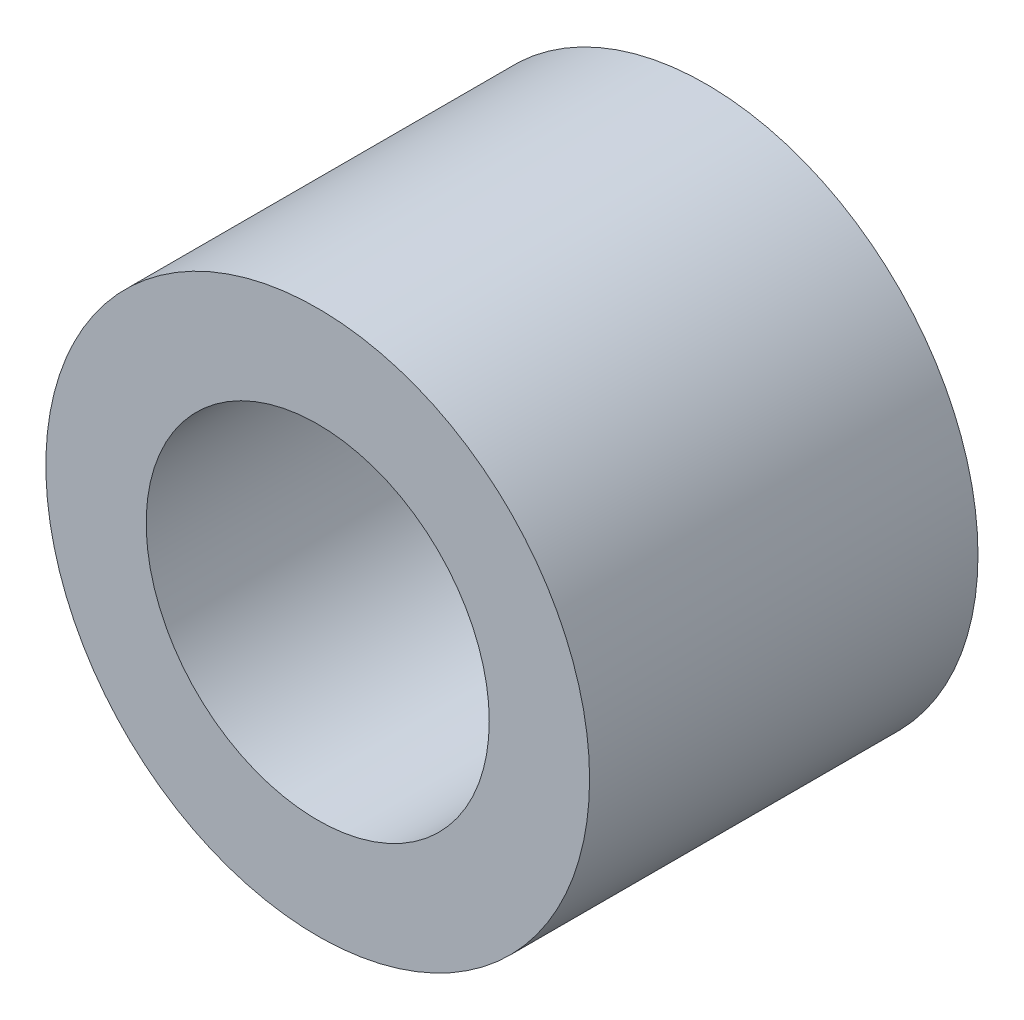
SolidWorks part; units mm, degrees
material "Латунь"
ref_plane "Спереди" through (0, 0, 0) normal (0, 0, 1) x (1, 0, 0)
ref_plane "Сверху" through (0, 0, 0) normal (0, 1, 0) x (1, 0, 0)
ref_plane "Справа" through (0, 0, 0) normal (1, 0, 0) x (0, 0, -1)
sketch "Эскиз7" plane through (0, 0, 0) normal (1, 0, 0) x (0, 0, -1)
  line L1 (0, 0) -> (3, 0)
  line L2 (0, 0) -> (0, 1.9)
  line L3 (0, 1.9) -> (3, 1.9)
  line L4 (3, 0) -> (3, 1.9)
  dimension "D1" = 3
  dimension "D2" = 1.9
revolve "Повернуть1" add sketch "Эскиз7" angle 360 about L1
hole_wizard "Отверстие обработанное метчиком M3x0.351" positions "Эскиз8" profile "Эскиз9" tap size "M3x0.35" standard "DIN" end condition through all
sketch "Эскиз8" plane through (0, 0, 0) normal (0, 0, 1) x (1, 0, 0)
  point P0 (0, 0)
sketch "Эскиз9" plane through (0, 0, 0) normal (1, 0, 0) x (0, -1, 0)
  line L0 (0, 0) -> (0, 3)
  line L1 (0, 3) -> (1.325, 3)
  line L2 (1.325, 3) -> (1.325, 0)
  line L5 (1.325, 0) -> (0, 0)
  line L11 (0, -6.35) -> (0, 107.95) construction
  dimension "Диаметр проходного сверла" = 2.65
  dimension "Глубина проходного сверла" = 3
cosmetic thread "Отверстие резьбы2" parameters "D2"=3
sketch "Эскиз45" plane through (0, 0, 0) normal (0, 0, 1) x (1, 0, 0)
  line L0 (0, 0) -> (0, 1.9) construction
  line L1 (0, 0.0356) -> (0, 0) construction
  line L2 (0, 0) -> (0.3647, 2.0681) construction
  line L3 (0, 2.1) -> (0, 0) construction
  line L4 (0, 2.1) -> (0, 1.8)
  line L5 (0.3126, 1.7727) -> (0.3647, 2.0681)
  line L6 (0.7182, 1.9734) -> (0.6156, 1.6914)
  line L7 (0.9, 1.5588) -> (1.05, 1.8187)
  line L8 (1.3499, 1.6087) -> (1.157, 1.3789)
  line L9 (1.3789, 1.157) -> (1.6087, 1.3499)
  line L10 (1.8187, 1.05) -> (1.5588, 0.9)
  line L11 (1.6914, 0.6156) -> (1.9734, 0.7182)
  line L12 (2.0681, 0.3647) -> (1.7727, 0.3126)
  line L13 (1.8, 0) -> (2.1, 0)
  line L14 (2.0681, -0.3647) -> (1.7727, -0.3126)
  line L15 (1.6914, -0.6156) -> (1.9734, -0.7182)
  line L16 (1.8187, -1.05) -> (1.5588, -0.9)
  line L17 (1.3789, -1.157) -> (1.6087, -1.3499)
  line L18 (1.3499, -1.6087) -> (1.157, -1.3789)
  line L19 (0.9, -1.5588) -> (1.05, -1.8187)
  line L20 (0.7182, -1.9734) -> (0.6156, -1.6914)
  line L21 (0.3126, -1.7727) -> (0.3647, -2.0681)
  line L22 (0, -2.1) -> (0, -1.8)
  line L23 (-0.3126, -1.7727) -> (-0.3647, -2.0681)
  line L24 (-0.7182, -1.9734) -> (-0.6156, -1.6914)
  line L25 (-0.9, -1.5588) -> (-1.05, -1.8187)
  line L26 (-1.3499, -1.6087) -> (-1.157, -1.3789)
  line L27 (-1.3789, -1.157) -> (-1.6087, -1.3499)
  line L28 (-1.8187, -1.05) -> (-1.5588, -0.9)
  line L29 (-1.6914, -0.6156) -> (-1.9734, -0.7182)
  line L30 (-2.0681, -0.3647) -> (-1.7727, -0.3126)
  line L31 (-1.8, 0) -> (-2.1, 0)
  line L32 (-2.0681, 0.3647) -> (-1.7727, 0.3126)
  line L33 (-1.6914, 0.6156) -> (-1.9734, 0.7182)
  line L34 (-1.8187, 1.05) -> (-1.5588, 0.9)
  line L35 (-1.3789, 1.157) -> (-1.6087, 1.3499)
  line L36 (-1.3499, 1.6087) -> (-1.157, 1.3789)
  line L37 (-0.9, 1.5588) -> (-1.05, 1.8187)
  line L38 (-0.7182, 1.9734) -> (-0.6156, 1.6914)
  line L39 (-0.3126, 1.7727) -> (-0.3647, 2.0681)
  arc A0 (0, 2.1) -> (0.3647, 2.0681) centre (0, 0) cw
  arc A1 (0.7182, 1.9734) -> (1.05, 1.8187) centre (0, 0) cw
  arc A2 (0.3126, 1.7727) -> (0, 1.8) centre (0, 0) ccw
  arc A3 (0.9, 1.5588) -> (0.6156, 1.6914) centre (0, 0) ccw
  arc A4 (1.3499, 1.6087) -> (1.6087, 1.3499) centre (0, 0) cw
  arc A5 (1.3789, 1.157) -> (1.157, 1.3789) centre (0, 0) ccw
  arc A6 (1.8187, 1.05) -> (1.9734, 0.7182) centre (0, 0) cw
  arc A7 (1.6914, 0.6156) -> (1.5588, 0.9) centre (0, 0) ccw
  arc A8 (2.0681, 0.3647) -> (2.1, 0) centre (0, 0) cw
  arc A9 (1.8, 0) -> (1.7727, 0.3126) centre (0, 0) ccw
  arc A10 (2.0681, -0.3647) -> (1.9734, -0.7182) centre (0, 0) cw
  arc A11 (1.6914, -0.6156) -> (1.7727, -0.3126) centre (0, 0) ccw
  arc A12 (1.8187, -1.05) -> (1.6087, -1.3499) centre (0, 0) cw
  arc A13 (1.3789, -1.157) -> (1.5588, -0.9) centre (0, 0) ccw
  arc A14 (1.3499, -1.6087) -> (1.05, -1.8187) centre (0, 0) cw
  arc A15 (0.9, -1.5588) -> (1.157, -1.3789) centre (0, 0) ccw
  arc A16 (0.7182, -1.9734) -> (0.3647, -2.0681) centre (0, 0) cw
  arc A17 (0.3126, -1.7727) -> (0.6156, -1.6914) centre (0, 0) ccw
  arc A18 (0, -2.1) -> (-0.3647, -2.0681) centre (0, 0) cw
  arc A19 (-0.3126, -1.7727) -> (0, -1.8) centre (0, 0) ccw
  arc A20 (-0.7182, -1.9734) -> (-1.05, -1.8187) centre (0, 0) cw
  arc A21 (-0.9, -1.5588) -> (-0.6156, -1.6914) centre (0, 0) ccw
  arc A22 (-1.3499, -1.6087) -> (-1.6087, -1.3499) centre (0, 0) cw
  arc A23 (-1.3789, -1.157) -> (-1.157, -1.3789) centre (0, 0) ccw
  arc A24 (-1.8187, -1.05) -> (-1.9734, -0.7182) centre (0, 0) cw
  arc A25 (-1.6914, -0.6156) -> (-1.5588, -0.9) centre (0, 0) ccw
  arc A26 (-2.0681, -0.3647) -> (-2.1, 0) centre (0, 0) cw
  arc A27 (-1.8, 0) -> (-1.7727, -0.3126) centre (0, 0) ccw
  arc A28 (-2.0681, 0.3647) -> (-1.9734, 0.7182) centre (0, 0) cw
  arc A29 (-1.6914, 0.6156) -> (-1.7727, 0.3126) centre (0, 0) ccw
  arc A30 (-1.8187, 1.05) -> (-1.6087, 1.3499) centre (0, 0) cw
  arc A31 (-1.3789, 1.157) -> (-1.5588, 0.9) centre (0, 0) ccw
  arc A32 (-1.3499, 1.6087) -> (-1.05, 1.8187) centre (0, 0) cw
  arc A33 (-0.9, 1.5588) -> (-1.157, 1.3789) centre (0, 0) ccw
  arc A34 (-0.7182, 1.9734) -> (-0.3647, 2.0681) centre (0, 0) cw
  arc A35 (-0.3126, 1.7727) -> (-0.6156, 1.6914) centre (0, 0) ccw
  point P79 (0, 0)
  dimension "D2" = 1.8
  dimension "D3" = 2.1
  dimension "D1" = 10
  dimension "D4" = 18
sketch "Эскиз48" plane through (0, 0, 0) normal (0, 0, 1) x (1, 0, 0)
  circle A0 centre (0, 0) radius 2.1
  circle A1 centre (0, 0) radius 1.9
  dimension "D1" = 3.8
  dimension "D2" = 4.2
extrude "Бобышка-Вытянуть1" add sketch "Эскиз48" against normal up to surface (3 mm away) up to face at (1.325, 0, -3)
extrude "Бобышка-Вытянуть2" [suppressed] add sketch "Эскиз45" against normal up to surface (3 mm away)
